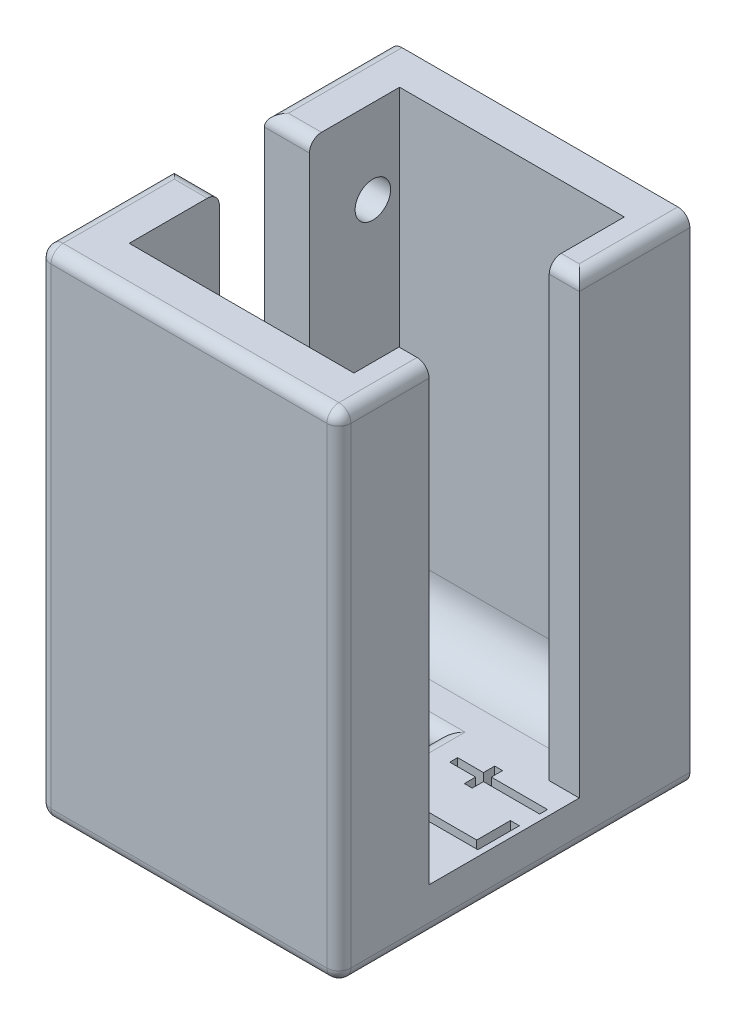
SolidWorks part; units mm, degrees
ref_plane "Front Plane" through (0, 0, 0) normal (0, 0, 1) x (1, 0, 0)
ref_plane "Top Plane" through (0, 0, 0) normal (0, 1, 0) x (1, 0, 0)
ref_plane "Right Plane" through (0, 0, 0) normal (1, 0, 0) x (0, 0, -1)
sketch "Sketch2" plane through (0, 0, 0) normal (0, 1, 0) x (1, 0, 0)
  line L0 (-9.5, -11.43) -> (9.5, -11.43)
  line L5 (12.04, -14.43) -> (-13.31, -14.43)
  line L10 (-13.31, -14.43) -> (-13.31, 15.24)
  line L15 (-13.31, 15.24) -> (12.04, 15.24)
  line L16 (12.04, 15.24) -> (12.04, 7.62)
  line L17 (12.04, -14.43) -> (12.04, -5.08)
  line L18 (12.04, 7.62) -> (9.5, 7.62)
  line L19 (9.5, 7.62) -> (9.5, 11.43)
  line L20 (9.5, 11.43) -> (-9.5, 11.43)
  line L21 (-9.5, 11.43) -> (-9.5, -11.43)
  line L22 (12.04, -5.08) -> (9.5, -5.08)
  line L24 (9.5, -11.43) -> (9.5, -5.08)
  point P6 (0, 11.43)
  point P12 (-9.5, 0)
  dimension "D1" = 22.86
  dimension "D2" = 19
  dimension "D3" = 3.81
  dimension "D4" = 3.81
  dimension "D5" = 7.62
  dimension "D6" = 2.54
  dimension "D7" = 5.08
  dimension "D8" = 3
extrude "Boss-Extrude2" add sketch "Sketch2" along normal blind 38.1
sketch "Sketch1" plane through (0, 0, 0) normal (0, 1, 0) x (1, 0, 0)
  line L1 (-13.31, -14.43) -> (12.04, -14.43)
  line L2 (-13.31, -14.43) -> (-13.31, 15.24)
  line L3 (-13.31, 15.24) -> (12.04, 15.24)
  line L4 (12.04, -14.43) -> (12.04, 15.24)
  point P0 (0, 0)
extrude "Boss-Extrude3" add sketch "Sketch1" against normal blind 3.81
sketch "Sketch3" plane through (0, 0, 0) normal (0, 1, 0) x (1, 0, 0)
  line L1 (-1.88, -3.81) -> (1.12, -3.81)
  line L2 (-1.88, -3.81) -> (-1.88, 3.81)
  line L3 (-1.88, 3.81) -> (1.12, 3.81)
  line L4 (1.12, -3.81) -> (1.12, 3.81)
  line L5 (-9.5, -11.43) -> (-9.5, 11.43) construction
  point P6 (-1.88, 0)
  dimension "D1" = 7.62
  dimension "D2" = 3
  dimension "D3" = 7.62
extrude "Cut-Extrude1" cut sketch "Sketch3" against normal through all
sketch "Sketch4" plane through (-9.5, 0, 0) normal (1, 0, 0) x (0, 0, -1)
  line L0 (-11.43, 38.1) -> (11.43, 38.1) construction
  line L1 (-3.81, 38.1) -> (3.81, 38.1)
  line L2 (-3.81, 38.1) -> (-3.81, 8)
  line L3 (-3.81, 8) -> (3.81, 8)
  line L4 (3.81, 38.1) -> (3.81, 8)
  line L5 (-11.43, 0) -> (11.43, 0) construction
  line L6 (-11.43, 38.1) -> (11.43, 38.1) construction
  point P10 (0, 38.1)
  point P11 (0, 38.1)
  dimension "D1" = 8
  dimension "D2" = 7.62
extrude "Cut-Extrude2" cut sketch "Sketch4" against normal through all
sketch "Sketch5" plane through (-9.5, 0, 0) normal (1, 0, 0) x (0, 0, -1)
  line L1 (-11.43, 0) -> (11.43, 0) construction
  circle A0 centre (-9.17, 31) radius 1.5
  circle A1 centre (8.23, 31) radius 1.5
  dimension "D3" = 3
  dimension "D1" = 2.26
  dimension "D2" = 17.4
  dimension "D4" = 31
extrude "Cut-Extrude3" cut sketch "Sketch5" against normal through all
sketch "Sketch6" plane through (0, 0, 14.43) normal (0, 0, 1) x (1, 0, 0)
  line L0 (-13.31, 38.1) -> (-13.31, -3.81) construction
  line L3 (-1.88, -3.81) -> (-1.88, 0) construction
  line L8 (12.04, 38.1) -> (12.04, 0) construction
  line L11 (-13.31, 38.1) -> (-9.5, 38.1) construction
  circle A0 centre (-11.405, 19.05) radius 1.45
  circle A1 centre (-3.81, -1.905) radius 1.45
  point P9 (-1.88, -1.905)
  point P20 (-11.405, 38.1)
  point P26 (12.04, 19.05)
  dimension "D1" = 2.9
  dimension "D2" = 9.5
extrude "Cut-Extrude4" cut sketch "Sketch6" against normal offset from surface (24.844 mm away) 6.604 up to face at (-11.405, 23.05, -3.81) offset beyond the face yes
fillet "Fillet1" radius 4 2 edges at (0, 0, -11.43) (0, 0, 11.43)
mirror "Mirror1" about plane through (0, 0, 0) normal (0, 0, 1) of bodies 106 120
delete or keep bodies "Body-Delete/Keep 1" type keep bodies bodies 116
fillet "Fillet4" radius 2.54 2 edges at (-11.405, 8, -3.81) (-11.405, 8, 3.81)
fillet "Fillet2" radius 1.016 11 edges at (-13.31, 17.145, 15.24) (12.04, 17.145, 15.24) (12.04, -3.81, 0.405) (-13.31, -3.81, 0.405) (-0.635, -3.81, 15.24) (12.04, 38.1, 11.43) (-0.635, 38.1, 15.24) (-13.31, 38.1, 9.525) (-13.31, 38.1, -9.12) (-11.405, 38.1, -3.81) (-11.405, 38.1, 3.81)
fillet "Fillet3" radius 1.27 4 edges at (-0.38, 0, -3.81) (-1.88, 0, 0) (-0.38, 0, 3.81) (1.12, 0, 0)
fillet "Fillet5" radius 1.016 2 edges at (12.04, 38.1, -9.755) (10.77, 38.1, -5.08)
ref_plane "Plane1" through (-15.85, 0, 0) normal (-1, 0, 0) x (0, 0, 1)
sketch "Sketch7" plane through (0, 0, 0) normal (0, 1, 0) x (1, 0, 0)
  line L0 (11.5383, -3.9427) -> (11.5383, 17.9144) construction
  text T0 "Lt\r\n" font "Century Gothic" height in points 28
extrude "Cut-Extrude5" cut sketch "Sketch7" against normal blind 1.27
equation "\".30.83in\"=0.83"
